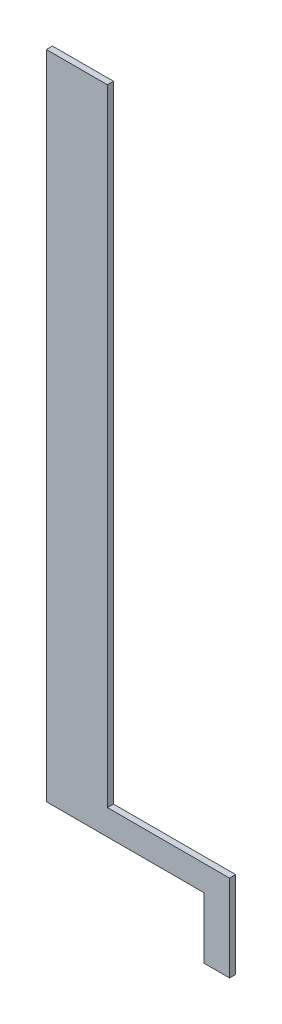
SolidWorks part; units mm, degrees
ref_plane "Front Plane" through (0, 0, 0) normal (0, 0, 1) x (1, 0, 0)
ref_plane "Top Plane" through (0, 0, 0) normal (0, 1, 0) x (1, 0, 0)
ref_plane "Right Plane" through (0, 0, 0) normal (1, 0, 0) x (0, 0, -1)
sketch "Sketch1" plane through (0, 0, 0) normal (0, 0, 1) x (1, 0, 0)
  line L0 (65, -147.5) -> (75, -147.5)
  line L1 (-15, 160) -> (15, 160)
  line L2 (-15, 160) -> (-15, -160)
  line L3 (-15, -160) -> (15, -160)
  line L4 (15, 160) -> (15, -147.5)
  line L5 (-15, 160) -> (15, -160) construction
  line L6 (-15, -160) -> (15, 160) construction
  line L7 (15, -160) -> (62.5, -160)
  line L9 (15, -147.5) -> (65, -147.5)
  line L10 (75, -160) -> (75, -147.5)
  line L13 (62.5, -160) -> (62.5, -190)
  line L14 (62.5, -190) -> (75, -190)
  line L15 (75, -160) -> (75, -190)
  point P0 (0, 0)
  dimension "D1" = 320
  dimension "D2" = 30
  dimension "D3" = 12.5
  dimension "D4" = 12.5
  dimension "D5" = 30
  dimension "D6" = 60
extrude "Boss-Extrude1" add sketch "Sketch1" along normal mid plane 3
